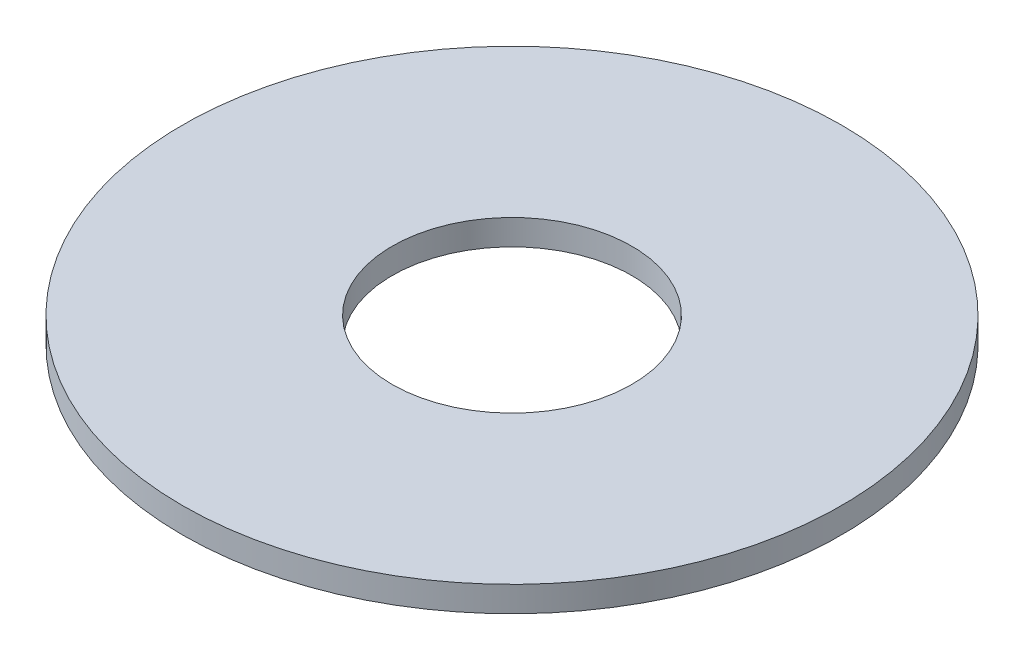
SolidWorks part; units mm, degrees
ref_plane "Front Plane" through (0, 0, 0) normal (0, 0, 1) x (1, 0, 0)
ref_plane "Top Plane" through (0, 0, 0) normal (0, 1, 0) x (1, 0, 0)
ref_plane "Right Plane" through (0, 0, 0) normal (1, 0, 0) x (0, 0, -1)
ref_plane "Plane1" through (0, 0, 0) normal (0, 0, -1) x (-1, 0, 0)
sketch "Sketch1" plane through (0, 0, 0) normal (0, 0, -1) x (-1, 0, 0)
  line L0 (-4, 0.85) -> (-11, 0.85)
  line L1 (-11, 0.85) -> (-11, 0)
  line L2 (-11, 0) -> (-4, 0)
  line L3 (-4, 0) -> (-4, 0.85)
  line L4 (0, 0) -> (0, 0.85) construction
revolve "Revolve1" add sketch "Sketch1" angle 360 about L4
